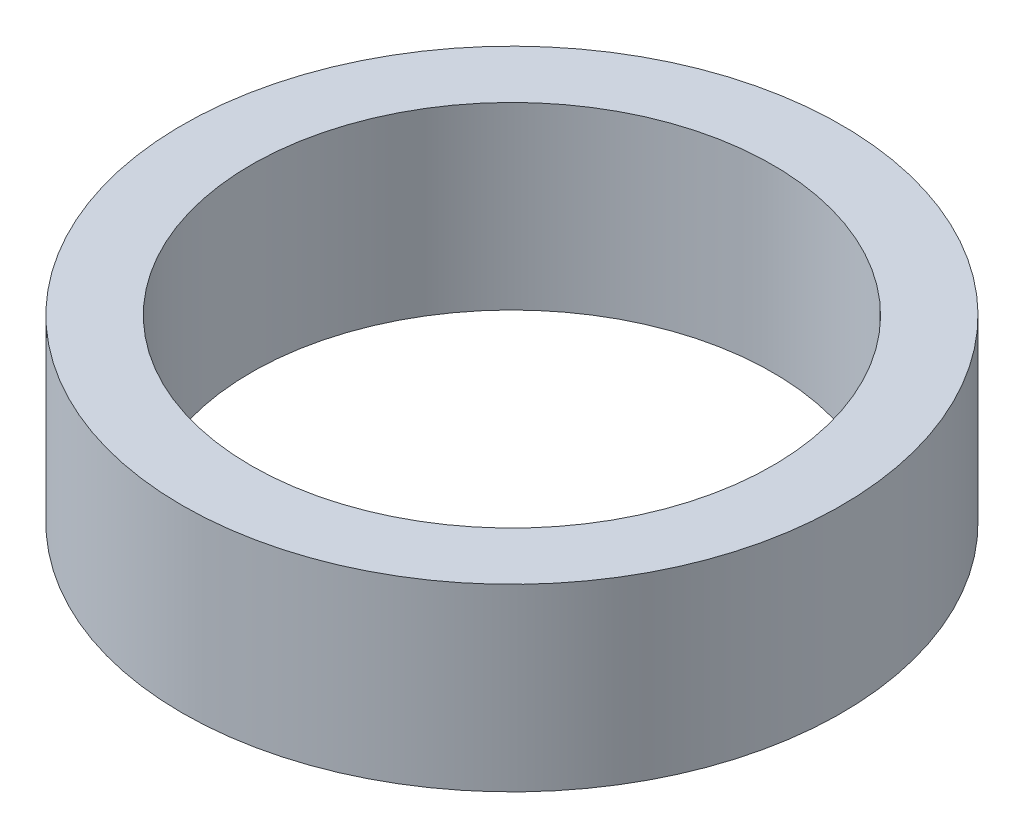
SolidWorks part; units mm, degrees
ref_plane "前视基准面" through (0, 0, 0) normal (0, 0, 1) x (1, 0, 0)
ref_plane "上视基准面" through (0, 0, 0) normal (0, 1, 0) x (1, 0, 0)
ref_plane "右视基准面" through (0, 0, 0) normal (1, 0, 0) x (0, 0, -1)
other "Configuration Table"
sketch "草图1" plane through (0, 0, 0) normal (0, 1, 0) x (1, 0, 0)
  circle A6 centre (-10.0999, 4.8989) radius 4.35
  circle A7 centre (-10.0999, 4.8989) radius 5.5
extrude "凸台-拉伸1" add sketch "草图1" along normal blind 3
